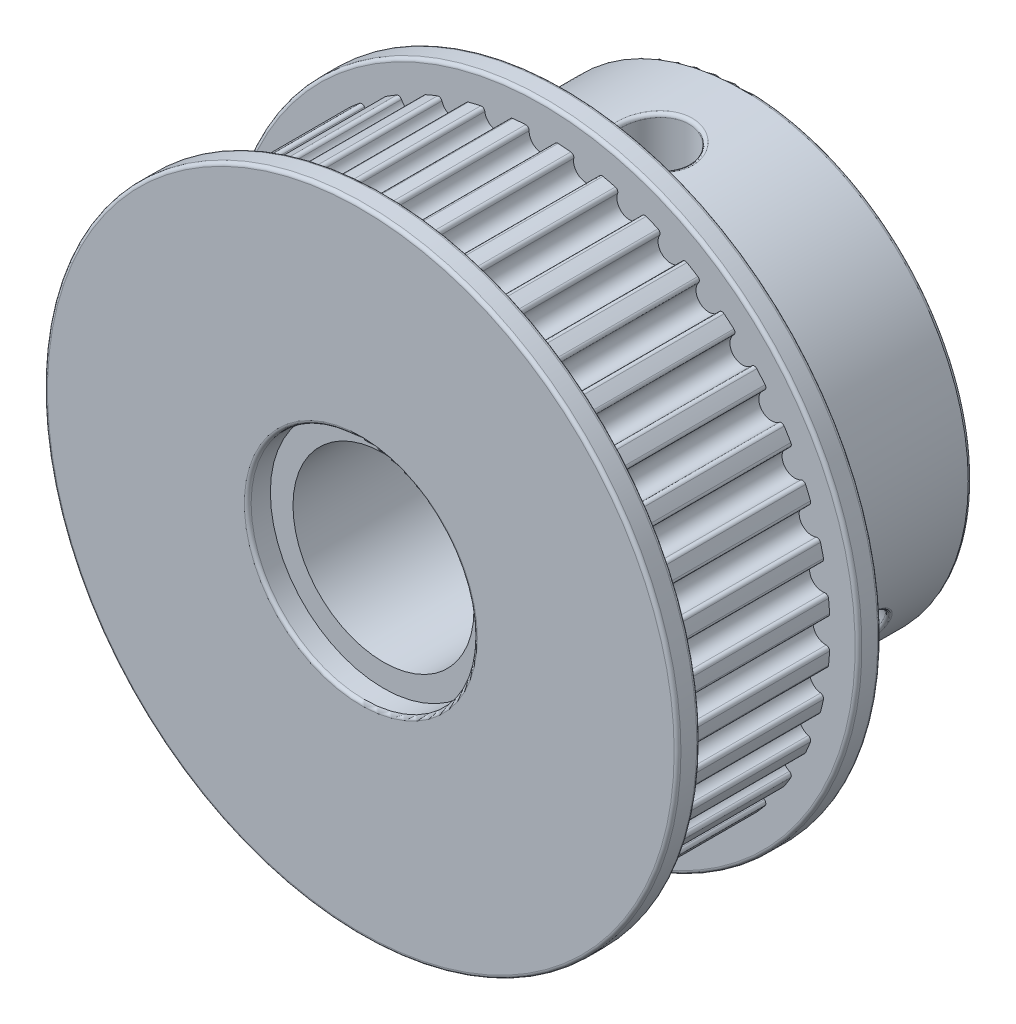
SolidWorks part; units mm, degrees
ref_plane "Ön Düzlem" through (0, 0, 0) normal (0, 0, 1) x (1, 0, 0)
ref_plane "Üst Düzlem" through (0, 0, 0) normal (0, 1, 0) x (1, 0, 0)
ref_plane "Sağ Düzlem" through (0, 0, 0) normal (1, 0, 0) x (0, 0, -1)
sketch "Çizim1" plane through (0, 0, 0) normal (0, 0, 1) x (1, 0, 0)
  arc A0 (-0.7182, 12.7186) -> (-1.2803, 12.6744) centre (0, 0) ccw
  circle A1 centre (0, 0) radius 4
  arc A2 (-0.5598, 12.5646) -> (0.5598, 12.5646) centre (0, 12.5489) ccw
  arc A3 (0.5598, 12.5646) -> (0.7182, 12.7186) centre (0.7097, 12.5688) cw
  arc A4 (-0.5598, 12.5646) -> (-0.7182, 12.7186) centre (-0.7097, 12.5688) ccw
  arc A5 (1.4127, 12.4975) -> (1.2803, 12.6744) centre (1.2652, 12.5251) ccw
  arc A6 (1.4127, 12.4975) -> (2.5184, 12.3224) centre (1.9631, 12.3944) ccw
  arc A7 (2.5184, 12.3224) -> (2.699, 12.4497) centre (2.6672, 12.3031) cw
  arc A8 (3.3503, 12.1226) -> (3.2472, 12.318) centre (3.209, 12.173) ccw
  arc A9 (3.3503, 12.1226) -> (4.4151, 11.7767) centre (3.8778, 11.9347) ccw
  arc A10 (4.4151, 11.7767) -> (4.6133, 11.8742) centre (4.559, 11.7344) cw
  arc A11 (5.2054, 11.4493) -> (5.1342, 11.6584) centre (5.0738, 11.5211) ccw
  arc A12 (5.2054, 11.4493) -> (6.203, 10.941) centre (5.6971, 11.1811) ccw
  arc A13 (6.203, 10.941) -> (6.414, 11.0063) centre (6.3385, 10.8767) cw
  arc A14 (6.9324, 10.494) -> (6.8948, 10.7117) centre (6.8136, 10.5856) ccw
  arc A15 (6.9324, 10.494) -> (7.8382, 9.836) centre (7.376, 10.1522) ccw
  arc A16 (7.8382, 9.836) -> (8.0568, 9.8674) centre (7.9619, 9.7512) cw
  arc A17 (8.4887, 9.2803) -> (8.4856, 9.5012) centre (8.3857, 9.3894) ccw
  arc A18 (8.4887, 9.2803) -> (9.2803, 8.4887) centre (8.8734, 8.8734) ccw
  arc A19 (9.2803, 8.4887) -> (9.5012, 8.4856) centre (9.3894, 8.3857) cw
  arc A20 (9.836, 7.8382) -> (9.8674, 8.0568) centre (9.7512, 7.9619) ccw
  arc A21 (9.836, 7.8382) -> (10.494, 6.9324) centre (10.1522, 7.376) ccw
  arc A22 (10.494, 6.9324) -> (10.7117, 6.8948) centre (10.5856, 6.8136) cw
  arc A23 (10.941, 6.203) -> (11.0063, 6.414) centre (10.8767, 6.3385) ccw
  arc A24 (10.941, 6.203) -> (11.4493, 5.2054) centre (11.1811, 5.6971) ccw
  arc A25 (11.4493, 5.2054) -> (11.6584, 5.1342) centre (11.5211, 5.0738) cw
  arc A26 (11.7767, 4.4151) -> (11.8742, 4.6133) centre (11.7344, 4.559) ccw
  arc A27 (11.7767, 4.4151) -> (12.1226, 3.3503) centre (11.9347, 3.8778) ccw
  arc A28 (12.1226, 3.3503) -> (12.318, 3.2472) centre (12.173, 3.209) cw
  arc A29 (12.3224, 2.5184) -> (12.4497, 2.699) centre (12.3031, 2.6672) ccw
  arc A30 (12.3224, 2.5184) -> (12.4975, 1.4127) centre (12.3944, 1.9631) ccw
  arc A31 (12.4975, 1.4127) -> (12.6744, 1.2803) centre (12.5251, 1.2652) cw
  arc A32 (12.5646, 0.5598) -> (12.7186, 0.7182) centre (12.5688, 0.7097) ccw
  arc A33 (12.5646, 0.5598) -> (12.5646, -0.5598) centre (12.5489, 0) ccw
  arc A34 (12.5646, -0.5598) -> (12.7186, -0.7182) centre (12.5688, -0.7097) cw
  arc A35 (12.4975, -1.4127) -> (12.6744, -1.2803) centre (12.5251, -1.2652) ccw
  arc A36 (12.4975, -1.4127) -> (12.3224, -2.5184) centre (12.3944, -1.9631) ccw
  arc A37 (12.3224, -2.5184) -> (12.4497, -2.699) centre (12.3031, -2.6672) cw
  arc A38 (12.1226, -3.3503) -> (12.318, -3.2472) centre (12.173, -3.209) ccw
  arc A39 (12.1226, -3.3503) -> (11.7767, -4.4151) centre (11.9347, -3.8778) ccw
  arc A40 (11.7767, -4.4151) -> (11.8742, -4.6133) centre (11.7344, -4.559) cw
  arc A41 (11.4493, -5.2054) -> (11.6584, -5.1342) centre (11.5211, -5.0738) ccw
  arc A42 (11.4493, -5.2054) -> (10.941, -6.203) centre (11.1811, -5.6971) ccw
  arc A43 (10.941, -6.203) -> (11.0063, -6.414) centre (10.8767, -6.3385) cw
  arc A44 (10.494, -6.9324) -> (10.7117, -6.8948) centre (10.5856, -6.8136) ccw
  arc A45 (10.494, -6.9324) -> (9.836, -7.8382) centre (10.1522, -7.376) ccw
  arc A46 (9.836, -7.8382) -> (9.8674, -8.0568) centre (9.7512, -7.9619) cw
  arc A47 (9.2803, -8.4887) -> (9.5012, -8.4856) centre (9.3894, -8.3857) ccw
  arc A48 (9.2803, -8.4887) -> (8.4887, -9.2803) centre (8.8734, -8.8734) ccw
  arc A49 (8.4887, -9.2803) -> (8.4856, -9.5012) centre (8.3857, -9.3894) cw
  arc A50 (7.8382, -9.836) -> (8.0568, -9.8674) centre (7.9619, -9.7512) ccw
  arc A51 (7.8382, -9.836) -> (6.9324, -10.494) centre (7.376, -10.1522) ccw
  arc A52 (6.9324, -10.494) -> (6.8948, -10.7117) centre (6.8136, -10.5856) cw
  arc A53 (6.203, -10.941) -> (6.414, -11.0063) centre (6.3385, -10.8767) ccw
  arc A54 (6.203, -10.941) -> (5.2054, -11.4493) centre (5.6971, -11.1811) ccw
  arc A55 (5.2054, -11.4493) -> (5.1342, -11.6584) centre (5.0738, -11.5211) cw
  arc A56 (4.4151, -11.7767) -> (4.6133, -11.8742) centre (4.559, -11.7344) ccw
  arc A57 (4.4151, -11.7767) -> (3.3503, -12.1226) centre (3.8778, -11.9347) ccw
  arc A58 (3.3503, -12.1226) -> (3.2472, -12.318) centre (3.209, -12.173) cw
  arc A59 (2.5184, -12.3224) -> (2.699, -12.4497) centre (2.6672, -12.3031) ccw
  arc A60 (2.5184, -12.3224) -> (1.4127, -12.4975) centre (1.9631, -12.3944) ccw
  arc A61 (1.4127, -12.4975) -> (1.2803, -12.6744) centre (1.2652, -12.5251) cw
  arc A62 (0.5598, -12.5646) -> (0.7182, -12.7186) centre (0.7097, -12.5688) ccw
  arc A63 (0.5598, -12.5646) -> (-0.5598, -12.5646) centre (0, -12.5489) ccw
  arc A64 (-0.5598, -12.5646) -> (-0.7182, -12.7186) centre (-0.7097, -12.5688) cw
  arc A65 (-1.4127, -12.4975) -> (-1.2803, -12.6744) centre (-1.2652, -12.5251) ccw
  arc A66 (-1.4127, -12.4975) -> (-2.5184, -12.3224) centre (-1.9631, -12.3944) ccw
  arc A67 (-2.5184, -12.3224) -> (-2.699, -12.4497) centre (-2.6672, -12.3031) cw
  arc A68 (-3.3503, -12.1226) -> (-3.2472, -12.318) centre (-3.209, -12.173) ccw
  arc A69 (-3.3503, -12.1226) -> (-4.4151, -11.7767) centre (-3.8778, -11.9347) ccw
  arc A70 (-4.4151, -11.7767) -> (-4.6133, -11.8742) centre (-4.559, -11.7344) cw
  arc A71 (-5.2054, -11.4493) -> (-5.1342, -11.6584) centre (-5.0738, -11.5211) ccw
  arc A72 (-5.2054, -11.4493) -> (-6.203, -10.941) centre (-5.6971, -11.1811) ccw
  arc A73 (-6.203, -10.941) -> (-6.414, -11.0063) centre (-6.3385, -10.8767) cw
  arc A74 (-6.9324, -10.494) -> (-6.8948, -10.7117) centre (-6.8136, -10.5856) ccw
  arc A75 (-6.9324, -10.494) -> (-7.8382, -9.836) centre (-7.376, -10.1522) ccw
  arc A76 (-7.8382, -9.836) -> (-8.0568, -9.8674) centre (-7.9619, -9.7512) cw
  arc A77 (-8.4887, -9.2803) -> (-8.4856, -9.5012) centre (-8.3857, -9.3894) ccw
  arc A78 (-8.4887, -9.2803) -> (-9.2803, -8.4887) centre (-8.8734, -8.8734) ccw
  arc A79 (-9.2803, -8.4887) -> (-9.5012, -8.4856) centre (-9.3894, -8.3857) cw
  arc A80 (-9.836, -7.8382) -> (-9.8674, -8.0568) centre (-9.7512, -7.9619) ccw
  arc A81 (-9.836, -7.8382) -> (-10.494, -6.9324) centre (-10.1522, -7.376) ccw
  arc A82 (-10.494, -6.9324) -> (-10.7117, -6.8948) centre (-10.5856, -6.8136) cw
  arc A83 (-10.941, -6.203) -> (-11.0063, -6.414) centre (-10.8767, -6.3385) ccw
  arc A84 (-10.941, -6.203) -> (-11.4493, -5.2054) centre (-11.1811, -5.6971) ccw
  arc A85 (-11.4493, -5.2054) -> (-11.6584, -5.1342) centre (-11.5211, -5.0738) cw
  arc A86 (-11.7767, -4.4151) -> (-11.8742, -4.6133) centre (-11.7344, -4.559) ccw
  arc A87 (-11.7767, -4.4151) -> (-12.1226, -3.3503) centre (-11.9347, -3.8778) ccw
  arc A88 (-12.1226, -3.3503) -> (-12.318, -3.2472) centre (-12.173, -3.209) cw
  arc A89 (-12.3224, -2.5184) -> (-12.4497, -2.699) centre (-12.3031, -2.6672) ccw
  arc A90 (-12.3224, -2.5184) -> (-12.4975, -1.4127) centre (-12.3944, -1.9631) ccw
  arc A91 (-12.4975, -1.4127) -> (-12.6744, -1.2803) centre (-12.5251, -1.2652) cw
  arc A92 (-12.5646, -0.5598) -> (-12.7186, -0.7182) centre (-12.5688, -0.7097) ccw
  arc A93 (-12.5646, -0.5598) -> (-12.5646, 0.5598) centre (-12.5489, 0) ccw
  arc A94 (-12.5646, 0.5598) -> (-12.7186, 0.7182) centre (-12.5688, 0.7097) cw
  arc A95 (-12.4975, 1.4127) -> (-12.6744, 1.2803) centre (-12.5251, 1.2652) ccw
  arc A96 (-12.4975, 1.4127) -> (-12.3224, 2.5184) centre (-12.3944, 1.9631) ccw
  arc A97 (-12.3224, 2.5184) -> (-12.4497, 2.699) centre (-12.3031, 2.6672) cw
  arc A98 (-12.1226, 3.3503) -> (-12.318, 3.2472) centre (-12.173, 3.209) ccw
  arc A99 (-12.1226, 3.3503) -> (-11.7767, 4.4151) centre (-11.9347, 3.8778) ccw
  arc A100 (-11.7767, 4.4151) -> (-11.8742, 4.6133) centre (-11.7344, 4.559) cw
  arc A101 (-11.4493, 5.2054) -> (-11.6584, 5.1342) centre (-11.5211, 5.0738) ccw
  arc A102 (-11.4493, 5.2054) -> (-10.941, 6.203) centre (-11.1811, 5.6971) ccw
  arc A103 (-10.941, 6.203) -> (-11.0063, 6.414) centre (-10.8767, 6.3385) cw
  arc A104 (-10.494, 6.9324) -> (-10.7117, 6.8948) centre (-10.5856, 6.8136) ccw
  arc A105 (-10.494, 6.9324) -> (-9.836, 7.8382) centre (-10.1522, 7.376) ccw
  arc A106 (-9.836, 7.8382) -> (-9.8674, 8.0568) centre (-9.7512, 7.9619) cw
  arc A107 (-9.2803, 8.4887) -> (-9.5012, 8.4856) centre (-9.3894, 8.3857) ccw
  arc A108 (-9.2803, 8.4887) -> (-8.4887, 9.2803) centre (-8.8734, 8.8734) ccw
  arc A109 (-8.4887, 9.2803) -> (-8.4856, 9.5012) centre (-8.3857, 9.3894) cw
  arc A110 (-7.8382, 9.836) -> (-8.0568, 9.8674) centre (-7.9619, 9.7512) ccw
  arc A111 (-7.8382, 9.836) -> (-6.9324, 10.494) centre (-7.376, 10.1522) ccw
  arc A112 (-6.9324, 10.494) -> (-6.8948, 10.7117) centre (-6.8136, 10.5856) cw
  arc A113 (-6.203, 10.941) -> (-6.414, 11.0063) centre (-6.3385, 10.8767) ccw
  arc A114 (-6.203, 10.941) -> (-5.2054, 11.4493) centre (-5.6971, 11.1811) ccw
  arc A115 (-5.2054, 11.4493) -> (-5.1342, 11.6584) centre (-5.0738, 11.5211) cw
  arc A116 (-4.4151, 11.7767) -> (-4.6133, 11.8742) centre (-4.559, 11.7344) ccw
  arc A117 (-4.4151, 11.7767) -> (-3.3503, 12.1226) centre (-3.8778, 11.9347) ccw
  arc A118 (-3.3503, 12.1226) -> (-3.2472, 12.318) centre (-3.209, 12.173) cw
  arc A119 (-2.5184, 12.3224) -> (-2.699, 12.4497) centre (-2.6672, 12.3031) ccw
  arc A120 (-2.5184, 12.3224) -> (-1.4127, 12.4975) centre (-1.9631, 12.3944) ccw
  arc A121 (-1.4127, 12.4975) -> (-1.2803, 12.6744) centre (-1.2652, 12.5251) cw
  arc A122 (1.2803, 12.6744) -> (0.7182, 12.7186) centre (0, 0) ccw
  arc A123 (3.2472, 12.318) -> (2.699, 12.4497) centre (0, 0) ccw
  arc A124 (5.1342, 11.6584) -> (4.6133, 11.8742) centre (0, 0) ccw
  arc A125 (6.8948, 10.7117) -> (6.414, 11.0063) centre (0, 0) ccw
  arc A126 (8.4856, 9.5012) -> (8.0568, 9.8674) centre (0, 0) ccw
  arc A127 (9.8674, 8.0568) -> (9.5012, 8.4856) centre (0, 0) ccw
  arc A128 (11.0063, 6.414) -> (10.7117, 6.8948) centre (0, 0) ccw
  arc A129 (11.8742, 4.6133) -> (11.6584, 5.1342) centre (0, 0) ccw
  arc A130 (12.4497, 2.699) -> (12.318, 3.2472) centre (0, 0) ccw
  arc A131 (12.7186, 0.7182) -> (12.6744, 1.2803) centre (0, 0) ccw
  arc A132 (12.6744, -1.2803) -> (12.7186, -0.7182) centre (0, 0) ccw
  arc A133 (12.318, -3.2472) -> (12.4497, -2.699) centre (0, 0) ccw
  arc A134 (11.6584, -5.1342) -> (11.8742, -4.6133) centre (0, 0) ccw
  arc A135 (10.7117, -6.8948) -> (11.0063, -6.414) centre (0, 0) ccw
  arc A136 (9.5012, -8.4856) -> (9.8674, -8.0568) centre (0, 0) ccw
  arc A137 (8.0568, -9.8674) -> (8.4856, -9.5012) centre (0, 0) ccw
  arc A138 (6.414, -11.0063) -> (6.8948, -10.7117) centre (0, 0) ccw
  arc A139 (4.6133, -11.8742) -> (5.1342, -11.6584) centre (0, 0) ccw
  arc A140 (2.699, -12.4497) -> (3.2472, -12.318) centre (0, 0) ccw
  arc A141 (0.7182, -12.7186) -> (1.2803, -12.6744) centre (0, 0) ccw
  arc A142 (-1.2803, -12.6744) -> (-0.7182, -12.7186) centre (0, 0) ccw
  arc A143 (-3.2472, -12.318) -> (-2.699, -12.4497) centre (0, 0) ccw
  arc A144 (-5.1342, -11.6584) -> (-4.6133, -11.8742) centre (0, 0) ccw
  arc A145 (-6.8948, -10.7117) -> (-6.414, -11.0063) centre (0, 0) ccw
  arc A146 (-8.4856, -9.5012) -> (-8.0568, -9.8674) centre (0, 0) ccw
  arc A147 (-9.8674, -8.0568) -> (-9.5012, -8.4856) centre (0, 0) ccw
  arc A148 (-11.0063, -6.414) -> (-10.7117, -6.8948) centre (0, 0) ccw
  arc A149 (-11.8742, -4.6133) -> (-11.6584, -5.1342) centre (0, 0) ccw
  arc A150 (-12.4497, -2.699) -> (-12.318, -3.2472) centre (0, 0) ccw
  arc A151 (-12.7186, -0.7182) -> (-12.6744, -1.2803) centre (0, 0) ccw
  arc A152 (-12.6744, 1.2803) -> (-12.7186, 0.7182) centre (0, 0) ccw
  arc A153 (-12.318, 3.2472) -> (-12.4497, 2.699) centre (0, 0) ccw
  arc A154 (-11.6584, 5.1342) -> (-11.8742, 4.6133) centre (0, 0) ccw
  arc A155 (-10.7117, 6.8948) -> (-11.0063, 6.414) centre (0, 0) ccw
  arc A156 (-9.5012, 8.4856) -> (-9.8674, 8.0568) centre (0, 0) ccw
  arc A157 (-8.0568, 9.8674) -> (-8.4856, 9.5012) centre (0, 0) ccw
  arc A158 (-6.414, 11.0063) -> (-6.8948, 10.7117) centre (0, 0) ccw
  arc A159 (-4.6133, 11.8742) -> (-5.1342, 11.6584) centre (0, 0) ccw
  arc A160 (-2.699, 12.4497) -> (-3.2472, 12.318) centre (0, 0) ccw
  point P286 (0, 0)
  dimension "D1" = 0.15
  dimension "D3" = 8
  dimension "D2" = 40
extrude "Yükseklik-Ekstrüzyon1" add sketch "Çizim1" along normal blind 7
sketch "Çizim2" plane through (0, 0, 7) normal (0, 0, 1) x (1, 0, 0)
  circle A0 centre (0, 0) radius 5
  circle A1 centre (0, 0) radius 14
  dimension "D1" = 28
extrude "Yükseklik-Ekstrüzyon2" add sketch "Çizim2" along normal blind 1
sketch "Çizim3" plane through (0, 0, 0) normal (0, 0, -1) x (-1, 0, 0)
  circle A0 centre (0, 0) radius 14
  circle A1 centre (0, 0) radius 4
  dimension "D1" = 8
extrude "Yükseklik-Ekstrüzyon3" add sketch "Çizim3" along normal blind 1
sketch "Çizim4" plane through (0, 0, -1) normal (0, 0, -1) x (-1, 0, 0)
  circle A0 centre (0, 0) radius 4
  circle A1 centre (0, 0) radius 10
  dimension "D1" = 8
extrude "Yükseklik-Ekstrüzyon4" add sketch "Çizim4" along normal blind 8
ref_plane "Düzlem1" through (0, 0, 0) normal (0, 1, 0) x (1, 0, 0)
sketch "Çizim5" plane through (0, 0, 0) normal (0, 1, 0) x (1, 0, 0)
  circle A0 centre (0, 5) radius 1.5
extrude "Kes-Ekstrüzyon1" cut sketch "Çizim5" along normal blind 11
pattern_circular "Dairesel Kaplama1" count 3 every 120 of "Kes-Ekstrüzyon1"
fillet "Radyus1" radius 0.15 10 edges at (5, 0, 8) (14, 0, 8) (14, 0, 7) (-14, 0, 0) (-14, 0, -1) (9.299, -3.6782, -4.6738) (-7.8349, -6.2141, -4.6738) (0.3261, 9.9947, -3.5359) (-10, 0, -9) (-4, 0, -9)
